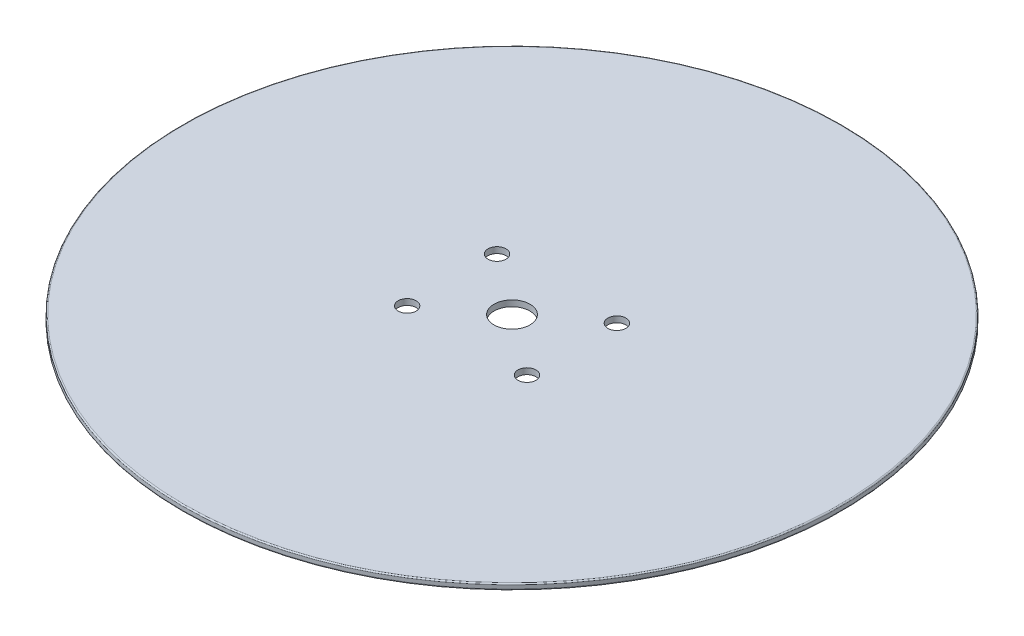
SolidWorks part; units mm, degrees
material "1060 Alloy"
ref_plane "Front Plane" through (0, 0, 0) normal (0, 0, 1) x (1, 0, 0)
ref_plane "Top Plane" through (0, 0, 0) normal (0, 1, 0) x (1, 0, 0)
ref_plane "Right Plane" through (0, 0, 0) normal (1, 0, 0) x (0, 0, -1)
sketch "Sketch1" plane through (0, 0, 0) normal (0, 1, 0) x (1, 0, 0)
  circle A0 centre (0, 0) radius 55
  dimension "D1" = 110
extrude "Boss-Extrude1" add sketch "Sketch1" along normal blind 1
fillet "Fillet2" radius 0.2 2 edges at (0, 1, 55) (0, 0, 55)
sketch "Sketch4" plane through (0, 1, 0) normal (0, 1, 0) x (1, 0, 0)
  circle A0 centre (0, 0) radius 3
  dimension "D1" = 6
extrude "Cut-Extrude2" cut sketch "Sketch4" against normal through all
sketch "Sketch3" plane through (0, 1, 0) normal (0, 1, 0) x (1, 0, 0)
  line L0 (0, 0) -> (10, 0)
  line L1 (0, 0) -> (-10, 0)
  line L2 (0, 7.5) -> (10, 7.5)
  line L3 (0, 7.5) -> (-10, 7.5)
  line L4 (0, -7.5) -> (10, -7.5)
  line L5 (0, -7.5) -> (-10, -7.5)
  circle A0 centre (-10, 7.5) radius 1.5
  circle A1 centre (10, 7.5) radius 1.5
  circle A2 centre (10, -7.5) radius 1.5
  circle A3 centre (-10, -7.5) radius 1.5
  dimension "D5" = 3
  dimension "D6" = 3
  dimension "D7" = 3
  dimension "D8" = 3
  dimension "D1" = 10
  dimension "D2" = 10
  dimension "D3" = 7.5
  dimension "D4" = 7.5
extrude "Cut-Extrude3" cut sketch "Sketch3" against normal through all
